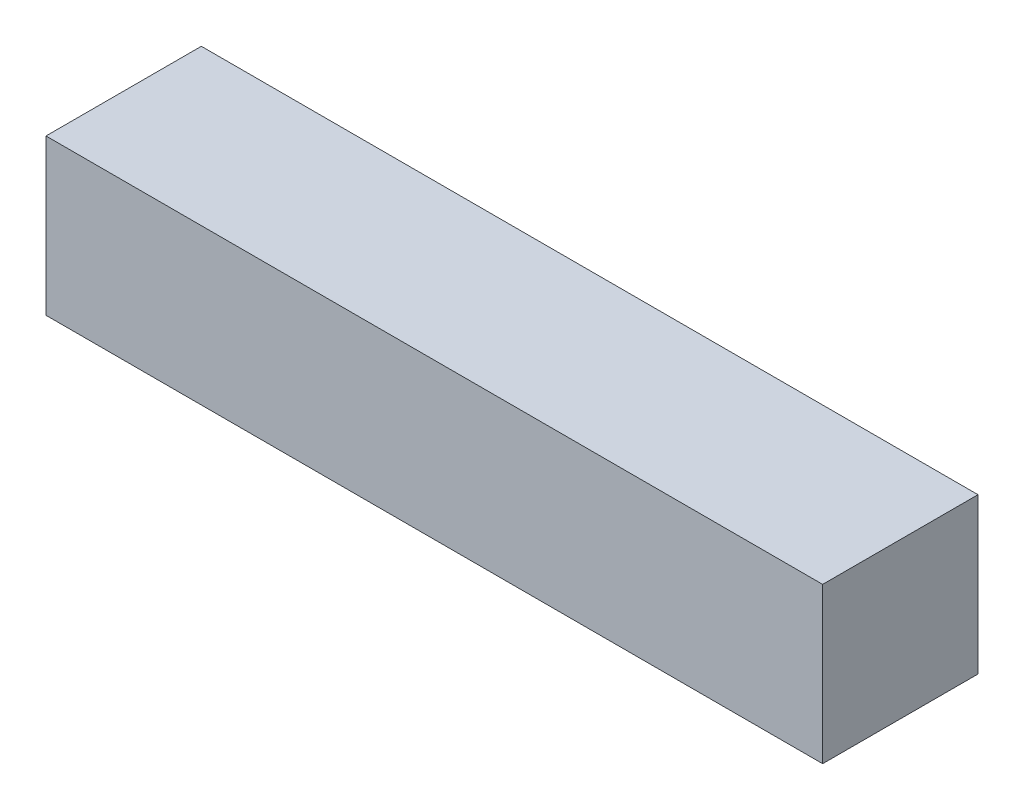
SolidWorks part; units mm, degrees
ref_plane "Front Plane" through (0, 0, 0) normal (0, 0, 1) x (1, 0, 0)
ref_plane "Top Plane" through (0, 0, 0) normal (0, 1, 0) x (1, 0, 0)
ref_plane "Right Plane" through (0, 0, 0) normal (1, 0, 0) x (0, 0, -1)
sketch "Sketch1" plane through (0, 0, 0) normal (1, 0, 0) x (0, 0, -1)
  line L1 (-12.7, -12.7) -> (12.7, -12.7)
  line L2 (-12.7, -12.7) -> (-12.7, 12.7)
  line L3 (-12.7, 12.7) -> (12.7, 12.7)
  line L4 (12.7, -12.7) -> (12.7, 12.7)
  line L5 (-12.7, -12.7) -> (12.7, 12.7) construction
  line L6 (-12.7, 12.7) -> (12.7, -12.7) construction
  point P0 (0, 0)
  dimension "D1" = 25.4
  dimension "D2" = 25.4
extrude "Boss-Extrude1" add sketch "Sketch1" along normal blind 127
